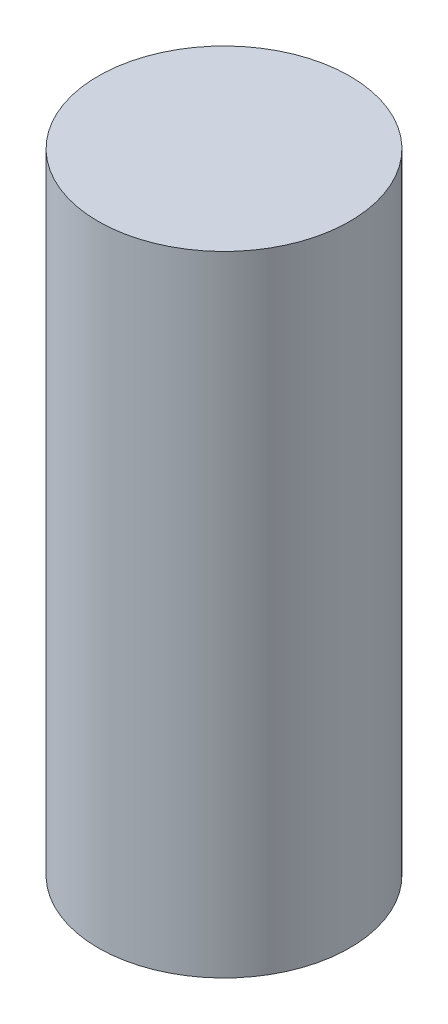
SolidWorks part; units mm, degrees
ref_plane "Alzado" through (0, 0, 0) normal (0, 0, 1) x (1, 0, 0)
ref_plane "Planta" through (0, 0, 0) normal (0, 1, 0) x (1, 0, 0)
ref_plane "Vista lateral" through (0, 0, 0) normal (1, 0, 0) x (0, 0, -1)
sketch "Sketch1" plane through (0, 0, 0) normal (0, 1, 0) x (1, 0, 0)
  circle A0 centre (0, 0) radius 4
  dimension "D1" = 8
extrude "Boss-Extrude1" add sketch "Sketch1" along normal blind 20
